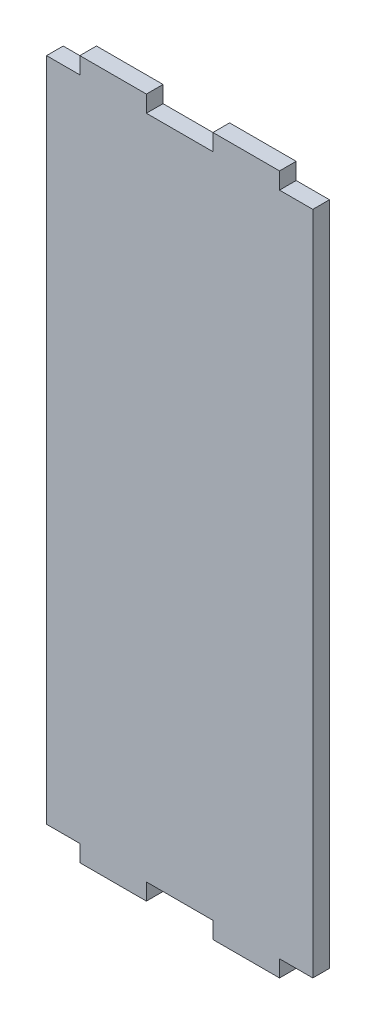
SolidWorks part; units mm, degrees
ref_plane "Front Plane" through (0, 0, 0) normal (0, 0, 1) x (1, 0, 0)
ref_plane "Top Plane" through (0, 0, 0) normal (0, 1, 0) x (1, 0, 0)
ref_plane "Right Plane" through (0, 0, 0) normal (1, 0, 0) x (0, 0, -1)
sketch "Sketch1" plane through (0, 0, 0) normal (0, 0, 1) x (1, 0, 0)
  line L1 (0, 0) -> (-80, 0)
  line L2 (0, 0) -> (0, 200)
  line L3 (0, 200) -> (-80, 200)
  line L4 (-80, 0) -> (-80, 200)
  dimension "D1" = 200
  dimension "D2" = 80
extrude "Boss-Extrude1" add sketch "Sketch1" along normal blind 5
sketch "Sketch2" plane through (0, 0, 5) normal (0, 0, 1) x (1, 0, 0)
  line L0 (0, 200) -> (-80, 200) construction
  line L1 (-10, 200) -> (-30, 200)
  line L2 (-10, 200) -> (-10, 205)
  line L3 (-10, 205) -> (-30, 205)
  line L4 (-30, 200) -> (-30, 205)
  line L5 (-80, 200) -> (-80, 0) construction
  line L6 (-50, 200) -> (-70, 200)
  line L7 (-50, 200) -> (-50, 205)
  line L8 (-50, 205) -> (-70, 205)
  line L9 (-70, 200) -> (-70, 205)
  line L10 (0, 0) -> (0, 200) construction
  line L11 (0, 100) -> (-18.6785, 100) construction
  line L12 (-70, 0) -> (-70, -5)
  line L13 (-50, -5) -> (-70, -5)
  line L14 (-50, 0) -> (-50, -5)
  line L15 (-50, 0) -> (-70, 0)
  line L16 (-30, 0) -> (-30, -5)
  line L17 (-10, -5) -> (-30, -5)
  line L18 (-10, 0) -> (-10, -5)
  line L19 (-10, 0) -> (-30, 0)
  dimension "D1" = 20
  dimension "D2" = 10
  dimension "D3" = 10
  dimension "D4" = 5
extrude "Boss-Extrude2" add sketch "Sketch2" against normal blind 5
